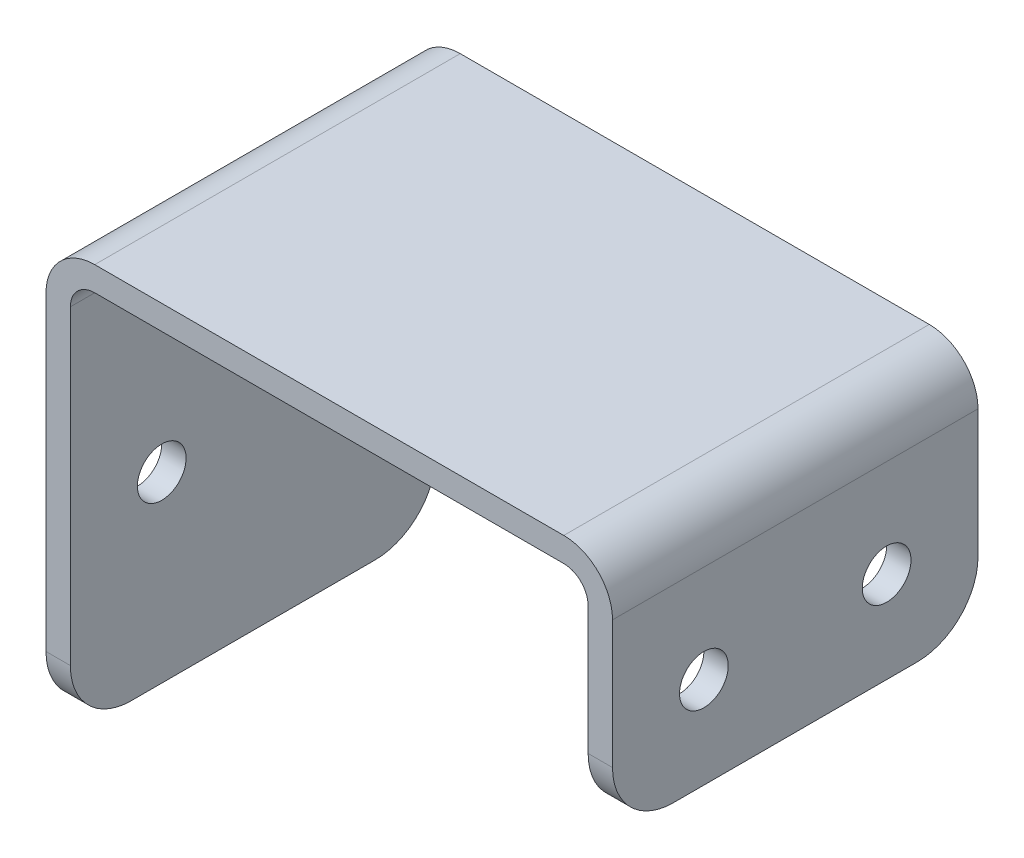
SolidWorks part; units mm, degrees
ref_plane "前视基准面" through (0, 0, 0) normal (0, 0, 1) x (1, 0, 0)
ref_plane "上视基准面" through (0, 0, 0) normal (0, 1, 0) x (1, 0, 0)
ref_plane "右视基准面" through (0, 0, 0) normal (1, 0, 0) x (0, 0, -1)
sketch "草图1" plane through (0, 0, 0) normal (0, 0, 1) x (1, 0, 0)
  line L0 (-42.5, 0) -> (42.5, 0) construction
  line L1 (-42.5, 0) -> (-42.5, 61)
  line L2 (-38.5, 65) -> (38.5, 65)
  line L3 (42.5, 61) -> (42.5, 30)
  line L4 (-46.5, 0) -> (-46.5, 61)
  line L5 (-38.5, 69) -> (38.5, 69)
  line L6 (46.5, 61) -> (46.5, 30)
  line L7 (-42.5, 0) -> (-46.5, 0)
  line L9 (-42.5, 65) -> (42.5, 65) construction
  line L10 (42.5, 65) -> (42.5, 0) construction
  line L11 (-42.5, 0) -> (-42.5, 65) construction
  line L12 (-46.5, 69) -> (46.5, 69) construction
  line L13 (46.5, 69) -> (46.5, 0) construction
  line L14 (-46.5, 0) -> (-46.5, 69) construction
  line L15 (42.5, 30) -> (46.5, 30)
  arc A0 (38.5, 65) -> (42.5, 61) centre (38.5, 61) cw
  arc A1 (-42.5, 61) -> (-38.5, 65) centre (-38.5, 61) cw
  arc A2 (38.5, 69) -> (46.5, 61) centre (38.5, 61) cw
  arc A3 (-46.5, 61) -> (-38.5, 69) centre (-38.5, 61) cw
  dimension "D4" = 4
  dimension "D5" = 8
  dimension "D1" = 4
  dimension "D2" = 85
  dimension "D3" = 65
  dimension "D6" = 30
extrude "凸台-拉伸1" add sketch "草图1" along normal blind 60
sketch "草图2" plane through (-46.5, 0, 0) normal (-1, 0, 0) x (0, 0, 1)
  line L0 (60, 0) -> (0, 0) construction
  line L1 (15, 30) -> (45, 30) construction
  line L2 (0, 61) -> (0, 0) construction
  circle A0 centre (15, 30) radius 4
  circle A1 centre (45, 30) radius 4
  dimension "D1" = 30
  dimension "D2" = 8
  dimension "D3" = 8
  dimension "D4" = 30
  dimension "D5" = 15
extrude "切除-拉伸1" cut sketch "草图2" against normal up to next
fillet "圆角1" radius 10 4 edges at (-44.5, 0, 60) (-44.5, 0, 0) (44.5, 30, 0) (44.5, 30, 60)
sketch "草图3" plane through (46.5, 0, 0) normal (1, 0, 0) x (0, 0, -1)
  line L0 (-50, 30) -> (-10, 30) construction
  line L2 (-60, 40) -> (-60, 61) construction
  line L3 (-45, 45) -> (-15, 45) construction
  circle A0 centre (-45, 45) radius 4
  circle A1 centre (-15, 45) radius 4
  dimension "D1" = 30
  dimension "D2" = 8
  dimension "D3" = 8
  dimension "D4" = 15
  dimension "D5" = 15
extrude "切除-拉伸2" cut sketch "草图3" against normal up to next
